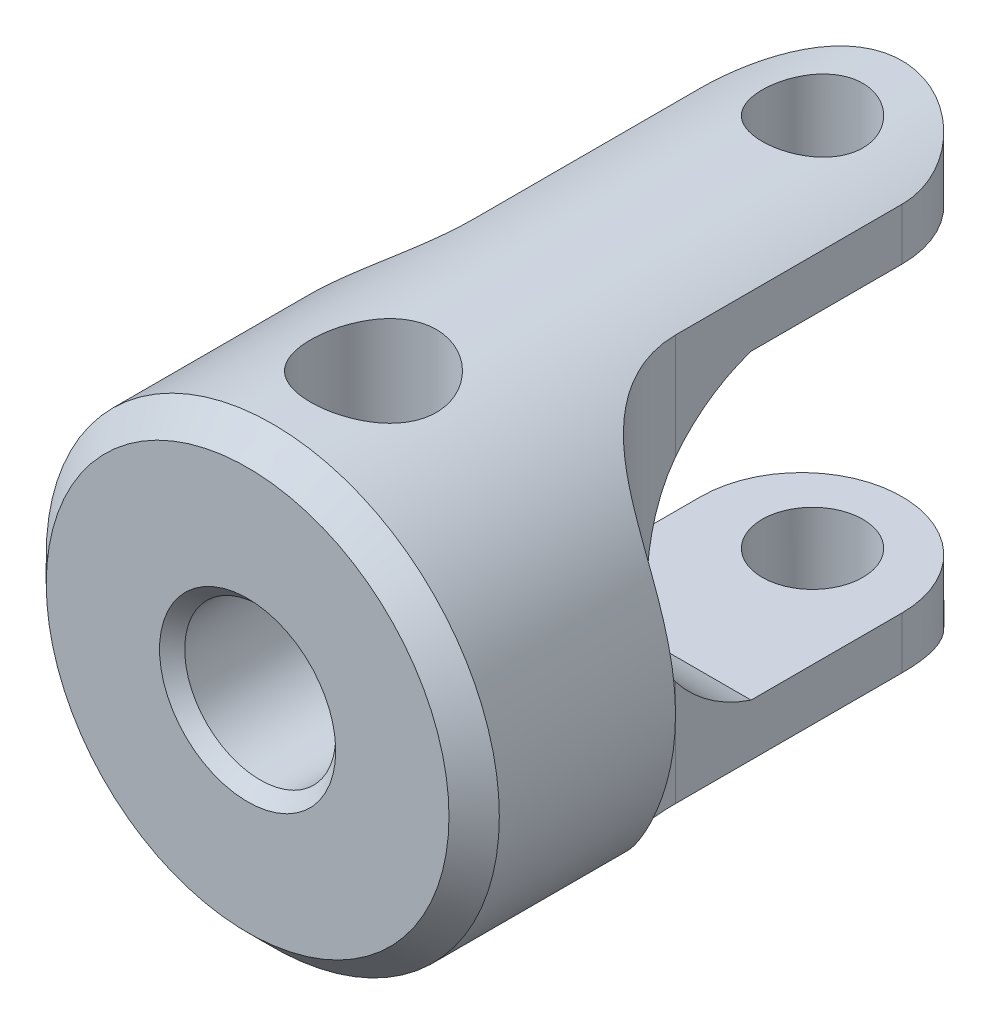
SolidWorks part; units mm, degrees
material "不锈钢 (铁素体)"
ref_plane "前视基准面" through (0, 0, 0) normal (0, 0, 1) x (1, 0, 0)
ref_plane "上视基准面" through (0, 0, 0) normal (0, 1, 0) x (1, 0, 0)
ref_plane "右视基准面" through (0, 0, 0) normal (1, 0, 0) x (0, 0, -1)
sketch "草图1" plane through (0, 0, 0) normal (0, 0, 1) x (1, 0, 0)
  circle A0 centre (0, 0) radius 4.5
extrude "凸台-拉伸1" add sketch "草图1" along normal blind 13
sketch "草图2" plane through (0, 0, 0) normal (0, 1, 0) x (1, 0, 0)
  line L0 (-4.5, 0) -> (-4.5, -13) construction
  line L1 (4.5, 0) -> (-4.5, 0) construction
  line L3 (-4.5, 0) -> (-4.5, -9)
  line L4 (4.5, 0) -> (-4.5, 0)
  line L5 (2, -2) -> (2, -6.5)
  line L6 (0, 0) -> (0, -13) construction
  line L7 (-2, -2) -> (-2, -6.5)
  line L8 (4.5, 0) -> (4.5, -9)
  arc A0 (2, -2) -> (-2, -2) centre (0, -2) ccw
  arc A1 (-4.5, -9) -> (-2, -6.5) centre (-4.5, -6.5) ccw
  arc A2 (4.5, -9) -> (2, -6.5) centre (4.5, -6.5) cw
  dimension "D1" = 2
  dimension "D2" = 4.5
extrude "切除-拉伸1" cut sketch "草图2" against normal mid plane 13 contours L3 A1 L7 A0 L4 | A2 L8 L4 A0 L5
sketch "草图3" plane through (0, 0, 0) normal (1, 0, 0) x (0, 0, -1)
  line L0 (0, -4.5) -> (0, 4.5) construction
  line L1 (0, 3) -> (-5, 3)
  line L2 (0, 3) -> (0, -3)
  line L3 (0, -3) -> (-5, -3)
  line L6 (0, 0) -> (-13, 0) construction
  line L7 (-13, 4.5) -> (-13, -4.5) construction
  arc A0 (-5, 3) -> (-5, -3) centre (-4, 0) ccw
  point P2 (-4, 0)
  dimension "D1" = 3
  dimension "D2" = 5
extrude "切除-拉伸2" cut sketch "草图3" against normal mid plane 13
sketch "草图4" plane through (0, 0, 0) normal (0, 1, 0) x (1, 0, 0)
  circle A0 centre (0, -1.7789) radius 1
extrude "切除-拉伸3" cut sketch "草图4" against normal mid plane 13
hole_wizard "打孔尺寸根据开槽半沉头木螺钉的类型1" positions "草图6" profile "草图5" countersink size "M3" standard "Gb" end condition through all
sketch "草图6" plane through (0, 0, 13) normal (0, 0, 1) x (1, 0, 0)
  point P0 (0, 0)
sketch "草图5" plane through (0, 0, 13) normal (1, 0, 0) x (0, -1, 0)
  line L0 (0, 0) -> (0, 13)
  line L1 (0, 13) -> (1.5, 13)
  line L2 (1.5, 13) -> (1.5, 0.25)
  line L3 (1.5, 0.25) -> (1.75, 0)
  line L5 (1.75, 0) -> (0, 0)
  line L6 (-1.5, 0.25) -> (-1.75, 0) construction
  line L11 (0, -6.35) -> (0, 107.95) construction
  dimension "通孔孔直径" = 3
  dimension "通孔孔深度" = 13
  dimension "近端锥形沉头孔直径" = 3.5
  dimension "近端锥形沉头孔角度" = 90
chamfer "倒角1" distance 0.5 angle 45 1 edges at (4.5, 0, 13)
ref_plane "基准面1" through (0, 4.5, 0) normal (0, 1, 0) x (1, 0, 0)
hole_wizard "M3 螺纹孔1" positions "草图8" profile "草图7" tap size "M3" standard "Gb"
sketch "草图8" plane through (0, 4.5, 0) normal (0, 1, 0) x (1, 0, 0)
  line L0 (-4, -13) -> (4, -13) construction
  point P0 (0, -10.5)
  dimension "D1" = 2.5
sketch "草图7" plane through (0, 4.5, 10.5) normal (1, 0, 0) x (0, 0, 1)
  line L0 (0, 0) -> (0, 3)
  line L1 (0, 3) -> (1.25, 3)
  line L2 (1.25, 3) -> (1.25, 0)
  line L5 (1.25, 0) -> (0, 0)
  line L11 (0, -6.35) -> (0, 107.95) construction
  dimension "通孔螺纹孔钻头直径" = 2.5
  dimension "通孔螺纹孔钻头深度" = 3
cosmetic thread "孔螺蚊线2" parameters "D2"=3
